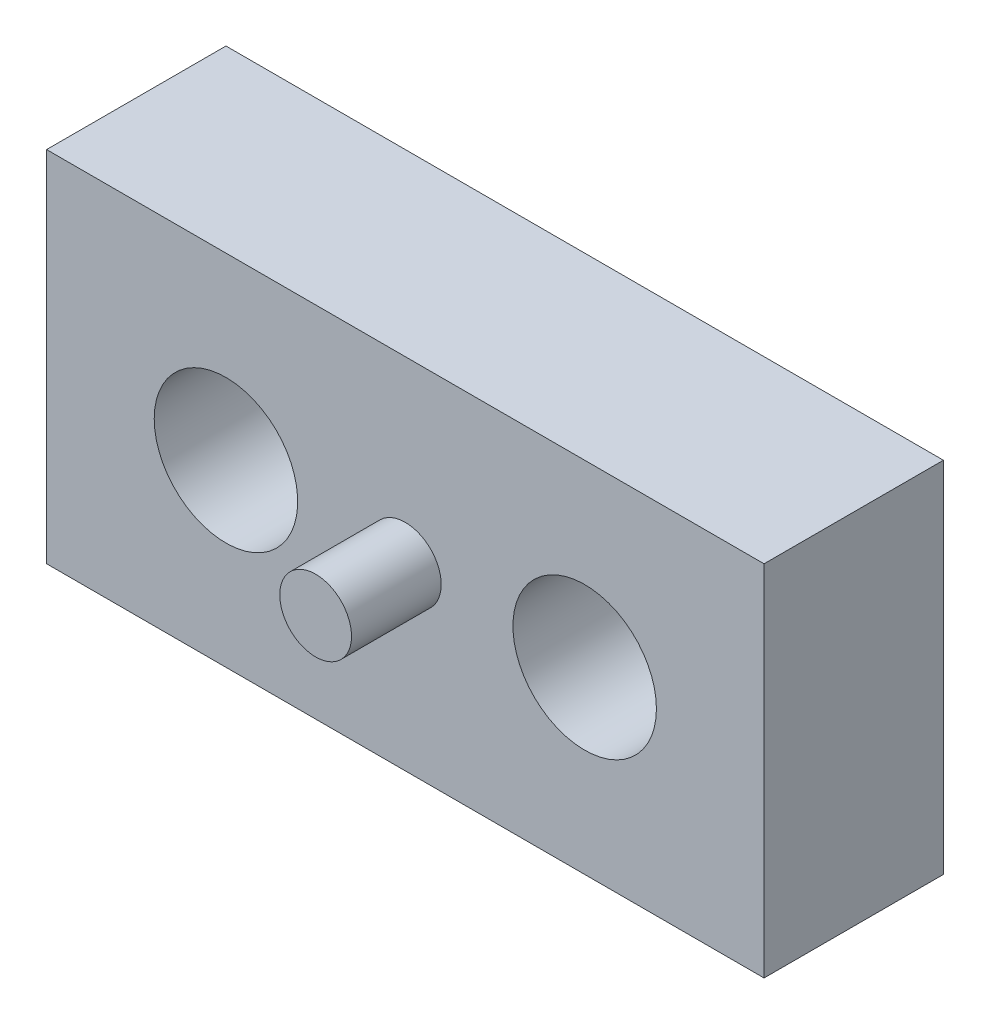
SolidWorks part; units mm, degrees
ref_plane "前视基准面" through (0, 0, 0) normal (0, 0, 1) x (1, 0, 0)
ref_plane "上视基准面" through (0, 0, 0) normal (0, 1, 0) x (1, 0, 0)
ref_plane "右视基准面" through (0, 0, 0) normal (1, 0, 0) x (0, 0, -1)
sketch "草图1" plane through (0, 0, 0) normal (0, 0, 1) x (1, 0, 0)
  line L0 (0, 0) -> (0, -21.9567) construction
  line L1 (-10, 5) -> (10, 5)
  line L2 (-10, 5) -> (-10, -5)
  line L3 (-10, -5) -> (10, -5)
  line L4 (10, 5) -> (10, -5)
  line L5 (-10, 5) -> (10, -5) construction
  line L6 (-10, -5) -> (10, 5) construction
  circle A0 centre (-5, 0) radius 1
  circle A1 centre (5, 0) radius 1
  point P0 (0, 0)
  dimension "D1" = 2
  dimension "D2" = 20
  dimension "D3" = 10
  dimension "D4" = 5
extrude "凸台-拉伸1" add sketch "草图1" along normal blind 5
sketch "草图2" plane through (0, 0, 5) normal (0, 0, 1) x (1, 0, 0)
  circle A0 centre (0, 0) radius 1
  dimension "D1" = 2
extrude "凸台-拉伸2" add sketch "草图2" along normal blind 2.5
sketch "草图4" plane through (0, 0, 5) normal (0, 0, 1) x (1, 0, 0)
  line L0 (0, 0) -> (0, -7.3571) construction
  circle A0 centre (5, 0) radius 2
  circle A1 centre (-5, 0) radius 2
  dimension "D1" = 4
extrude "切除-拉伸2" cut sketch "草图4" against normal blind 3
